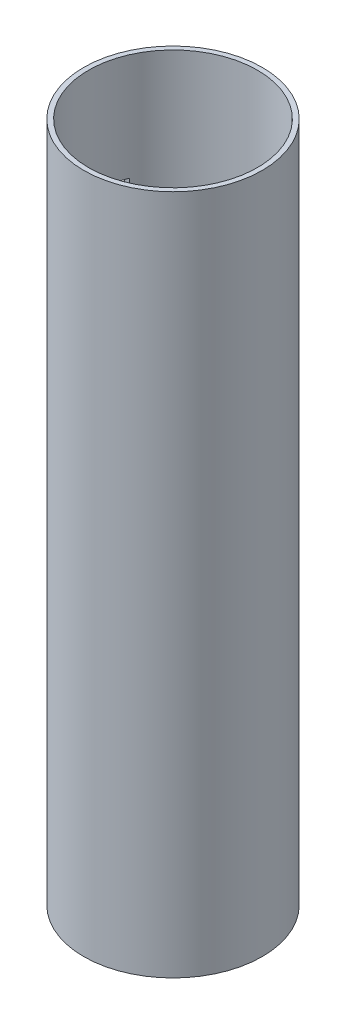
SolidWorks part; units mm, degrees
ref_plane "Front Plane" through (0, 0, 0) normal (0, 0, 1) x (1, 0, 0)
ref_plane "Top Plane" through (0, 0, 0) normal (0, 1, 0) x (1, 0, 0)
ref_plane "Right Plane" through (0, 0, 0) normal (1, 0, 0) x (0, 0, -1)
sketch "Sketch1" plane through (0, 0, 0) normal (0, 1, 0) x (1, 0, 0)
  circle A0 centre (0, 0) radius 47.0842
  dimension "D1" = 94.1685
extrude "Boss-Extrude1" add sketch "Sketch1" along normal blind 359.156
shell "Shell1" thickness 2.54
sketch "Sketch2" plane through (0, 0, 0) normal (1, 0, 0) x (0, 0, -1)
  line L1 (-13.1701, 302.6949) -> (17.8737, 302.6949)
  line L2 (-13.1701, 302.6949) -> (-13.1701, 237.7851)
  line L3 (-13.1701, 237.7851) -> (17.8737, 237.7851)
  line L4 (17.8737, 302.6949) -> (17.8737, 237.7851)
  dimension "D1" = 13.1701
  dimension "D2" = 64.9098
  dimension "D3" = 237.7851
  dimension "D4" = 17.8737
extrude "Cut-Extrude1" cut sketch "Sketch2" against normal blind 359.156
